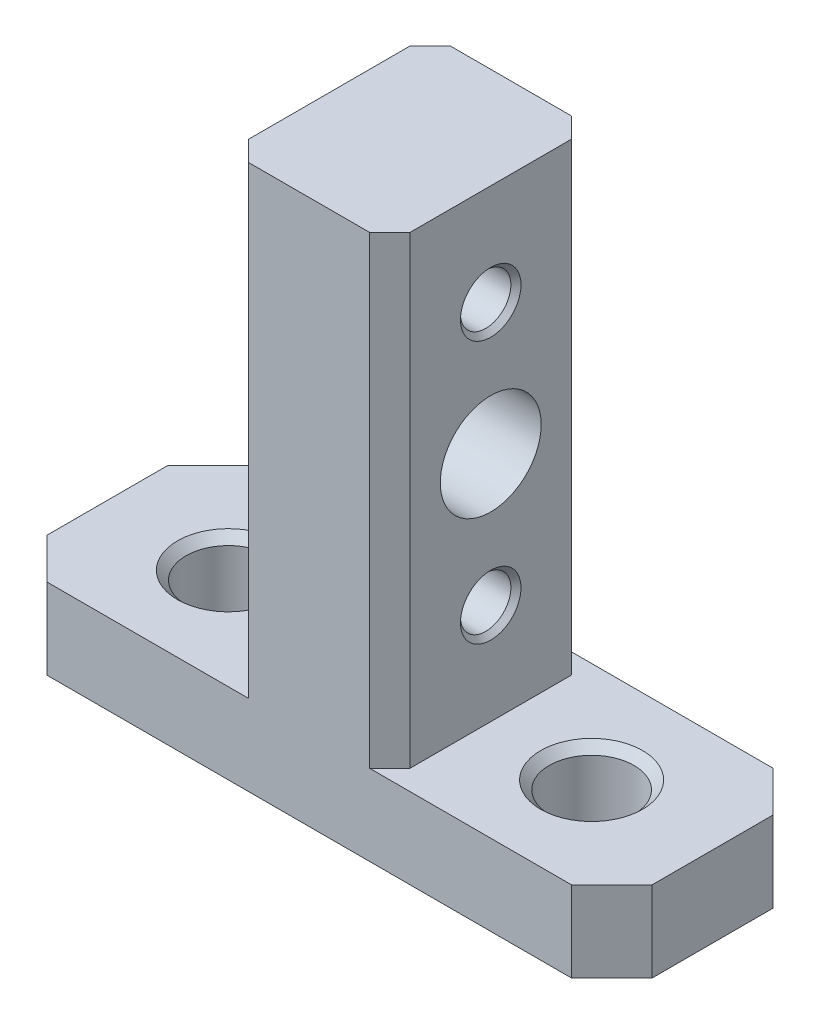
SolidWorks part; units mm, degrees
ref_plane "前视基准面" through (0, 0, 0) normal (0, 0, 1) x (1, 0, 0)
ref_plane "上视基准面" through (0, 0, 0) normal (0, 1, 0) x (1, 0, 0)
ref_plane "右视基准面" through (0, 0, 0) normal (1, 0, 0) x (0, 0, -1)
sketch "草图1" plane through (0, 0, 0) normal (0, 0, 1) x (1, 0, 0)
  line L0 (-41.5733, -4.0396) -> (-41.5733, -8.0396)
  line L1 (-41.5733, -8.0396) -> (-11.5733, -8.0396)
  line L2 (-11.5733, -8.0396) -> (-11.5733, -4.0396)
  line L6 (-41.5733, -4.0396) -> (-30.5733, -4.0396)
  line L7 (-22.5733, -4.0396) -> (-11.5733, -4.0396)
  line L8 (-22.5733, -4.0396) -> (-22.5733, 18.9604)
  line L9 (-22.5733, 18.9604) -> (-30.5733, 18.9604)
  line L10 (-30.5733, 18.9604) -> (-30.5733, -4.0396)
extrude "凸台-拉伸1" add sketch "草图1" along normal blind 10
sketch "草图2" plane through (0, -4.0396, 0) normal (0, 1, 0) x (1, 0, 0)
  line L0 (-11.5733, 0) -> (-22.5733, 0) construction
  line L1 (-11.5733, -10) -> (-11.5733, 0) construction
  line L2 (-41.5733, -10) -> (-41.5733, 0) construction
  point P0 (-17.5733, -5)
  point P5 (-35.5733, -5)
  point P13 (-17.5733, -5)
  point P14 (-35.5733, -5)
  dimension "D1" = 5
  dimension "D2" = 6
  dimension "D3" = 6
chamfer "倒角1" distance 2 angle 45 4 edges at (-11.5733, -6.0396, 10) (-11.5733, -6.0396, 0) (-41.5733, -6.0396, 10) (-41.5733, -6.0396, 0)
chamfer "倒角2" distance 1 angle 45 4 edges at (-22.5733, 7.4604, 10) (-30.5733, 7.4604, 10) (-30.5733, 7.4604, 0) (-22.5733, 7.4604, 0)
sketch "草图3" plane through (-22.5733, 0, 0) normal (1, 0, 0) x (0, 0, -1)
  line L4 (0, 18.9604) -> (0, -4.0396) construction
  line L6 (-9, 18.9604) -> (-1, 18.9604) construction
  circle A0 centre (-5, 7.4604) radius 2.5
  point P0 (-5, 7.4604)
  dimension "D1" = 5
  dimension "D2" = 11.5
extrude "切除-拉伸2" cut sketch "草图3" against normal up to next
sketch "草图4" plane through (-22.5733, 0, 0) normal (1, 0, 0) x (0, 0, -1)
  line L0 (0, 18.9604) -> (0, -4.0396) construction
  circle A0 centre (-5, 7.4604) radius 2.5 construction
  point P0 (-5, 0.9604)
  point P1 (-5, 13.9604)
  dimension "D1" = 6.5
  dimension "D2" = 5
  dimension "D3" = 6.5
hole_wizard "M3 螺纹孔1" positions "3D草图2" profile "草图6" tap size "M3" standard "GB" end condition up to next
sketch3d "3D草图2"
  point P0 (-22.5733, 13.9604, 5)
  point P3 (-22.5733, 0.9604, 5)
sketch "草图6" plane through (-22.5733, 13.9604, 5) normal (0, 1, 0) x (0, 0, -1)
  line L0 (0, 0) -> (0, 8)
  line L1 (0, 8) -> (1.25, 8)
  line L2 (1.25, 8) -> (1.25, 0.25)
  line L3 (1.25, 0.25) -> (1.5, 0)
  line L5 (1.5, 0) -> (0, 0)
  line L6 (-1.25, 0.25) -> (-1.5, 0) construction
  line L11 (0, -6.35) -> (0, 107.95) construction
  dimension "通孔螺纹孔钻头直径" = 2.5
  dimension "通孔螺纹孔钻头深度" = 8
  dimension "近端锥形沉头孔直径" = 3
  dimension "近端锥形沉头孔角度" = 90
cosmetic thread "孔螺蚊线1" parameters "D2"=3
cosmetic thread "孔螺蚊线2" parameters "D2"=3
hole_wizard "M5 螺纹孔1" positions "3D草图3" profile "草图7" tap size "M5" standard "KS" end condition up to next
sketch3d "3D草图3"
  point P0 (-35.5733, -4.0396, 5)
  point P3 (-17.5733, -4.0396, 5)
sketch "草图7" plane through (-35.5733, -4.0396, 5) normal (1, 0, 0) x (0, 0, 1)
  line L0 (0, 0) -> (0, 4)
  line L1 (0, 4) -> (2.1, 4)
  line L2 (2.1, 4) -> (2.1, 0.425)
  line L3 (2.1, 0.425) -> (2.525, 0)
  line L5 (2.525, 0) -> (0, 0)
  line L6 (-2.1, 0.425) -> (-2.525, 0) construction
  line L11 (0, -6.35) -> (0, 107.95) construction
  dimension "通孔螺纹孔钻头直径" = 4.2
  dimension "通孔螺纹孔钻头深度" = 4
  dimension "近端锥形沉头孔直径" = 5.05
  dimension "近端锥形沉头孔角度" = 90
cosmetic thread "孔螺蚊线3" parameters "D2"=5
cosmetic thread "孔螺蚊线4" parameters "D2"=5
